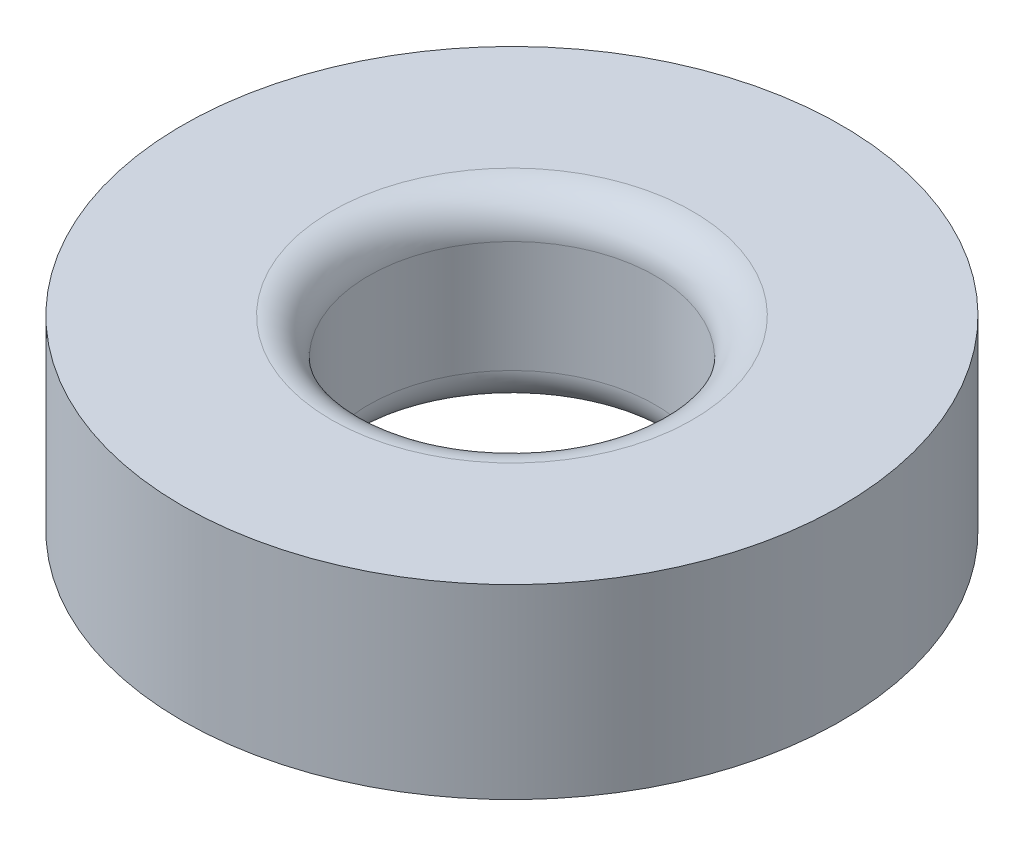
SolidWorks part; units mm, degrees
ref_plane "Front Plane" through (0, 0, 0) normal (0, 0, 1) x (1, 0, 0)
ref_plane "Top Plane" through (0, 0, 0) normal (0, 1, 0) x (1, 0, 0)
ref_plane "Right Plane" through (0, 0, 0) normal (1, 0, 0) x (0, 0, -1)
sketch "Sketch2" plane through (0, 0, 0) normal (0, 1, 0) x (1, 0, 0)
  circle A0 centre (0, 0) radius 3.85
  circle A1 centre (0, 0) radius 8.85
  dimension "D1" = 7.7
  dimension "D2" = 5
extrude "Boss-Extrude1" add sketch "Sketch2" along normal blind 5
fillet "Fillet1" radius 1 2 edges at (0, 0, 3.85) (0, 5, 3.85)
